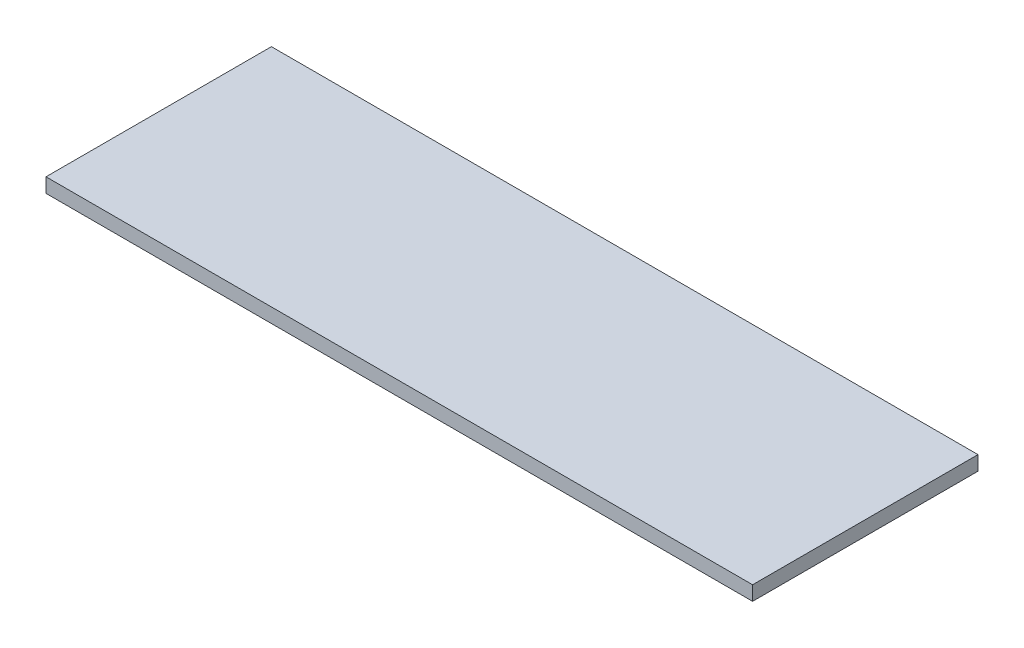
SolidWorks part; units mm, degrees
ref_plane "Спереди" through (0, 0, 0) normal (0, 0, 1) x (1, 0, 0)
ref_plane "Сверху" through (0, 0, 0) normal (0, 1, 0) x (1, 0, 0)
ref_plane "Справа" through (0, 0, 0) normal (1, 0, 0) x (0, 0, -1)
sketch "Эскиз1" plane through (0, 0, 0) normal (0, 1, 0) x (1, 0, 0)
  line L1 (442, -141) -> (-442, -141)
  line L2 (442, -141) -> (442, 141)
  line L3 (442, 141) -> (-442, 141)
  line L4 (-442, -141) -> (-442, 141)
  line L5 (442, -141) -> (-442, 141) construction
  line L6 (442, 141) -> (-442, -141) construction
  point P0 (0, 0)
  dimension "D1" = 884
  dimension "D2" = 282
extrude "Бобышка-Вытянуть1" add sketch "Эскиз1" along normal blind 18
